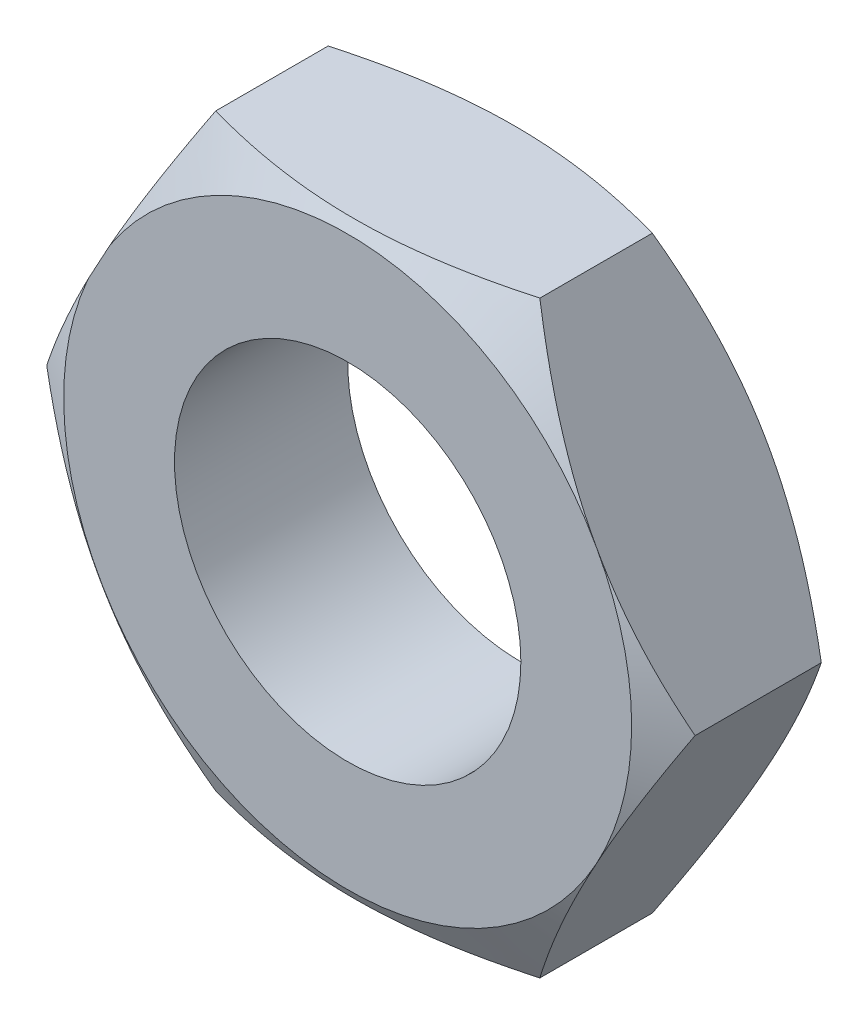
SolidWorks part; units mm, degrees
ref_plane "Front Plane" through (0, 0, 0) normal (0, 0, 1) x (1, 0, 0)
ref_plane "Top Plane" through (0, 0, 0) normal (0, 1, 0) x (1, 0, 0)
ref_plane "Right Plane" through (0, 0, 0) normal (1, 0, 0) x (0, 0, -1)
sketch "Sketch1" plane through (0, 0, 0) normal (0, 0, 1) x (1, 0, 0)
  line L0 (-14.6891, 0) -> (16.0354, 0) construction
  line L1 (9.3597, 0) -> (4.68, 8.5)
  line L2 (4.68, 8.5) -> (-4.68, 8.5)
  line L3 (-4.68, 8.5) -> (-9.36, -0.106)
  line L4 (-9.36, -0.106) -> (-4.68, -8.5)
  line L5 (-4.68, -8.5) -> (4.68, -8.5)
  line L6 (4.68, -8.5) -> (9.3597, 0)
  dimension "D1" = 18.72
  dimension "D2" = 8.5
  dimension "D3" = 8.5
extrude "Boss-Extrude1" add sketch "Sketch1" along normal blind 5 contours L2 L3 L4 L5 L6 L1
sketch "Sketch2" plane through (0, 0, 5) normal (0, 0, 1) x (1, 0, 0)
  circle A0 centre (0, 0) radius 8.1992
extrude "Cut-Extrude1" cut sketch "Sketch2" against normal blind 10 draft 60 flip side to cut
sketch "Sketch3" plane through (0, 0, 0) normal (0, 0, -1) x (-1, 0, 0)
  circle A0 centre (0, 0) radius 8.1722
extrude "Cut-Extrude2" cut sketch "Sketch3" against normal blind 1 draft 60 flip side to cut
sketch "Sketch4" plane through (0, 0, 5) normal (0, 0, 1) x (1, 0, 0)
  circle A0 centre (0, 0) radius 5
  dimension "D1" = 10
extrude "Cut-Extrude3" cut sketch "Sketch4" against normal blind 8
